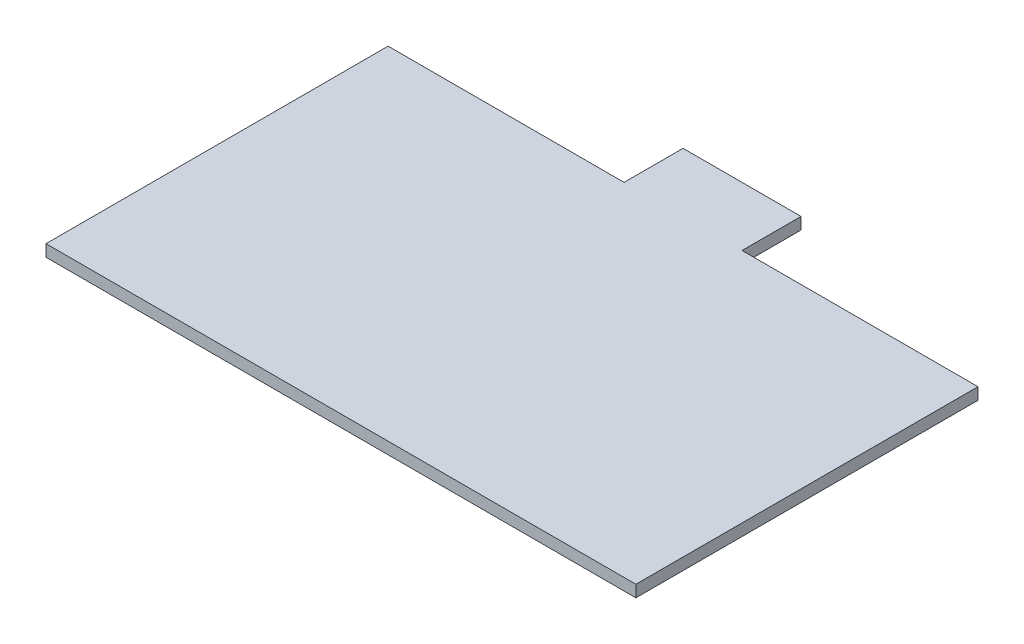
SolidWorks part; units mm, degrees
ref_plane "Front Plane" through (0, 0, 0) normal (0, 0, 1) x (1, 0, 0)
ref_plane "Top Plane" through (0, 0, 0) normal (0, 1, 0) x (1, 0, 0)
ref_plane "Right Plane" through (0, 0, 0) normal (1, 0, 0) x (0, 0, -1)
sketch "Sketch1" plane through (0, 0, 0) normal (0, 1, 0) x (1, 0, 0)
  line L1 (25, -14.5) -> (-25, -14.5)
  line L2 (25, -14.5) -> (25, 14.5)
  line L3 (25, 14.5) -> (-25, 14.5)
  line L4 (-25, -14.5) -> (-25, 14.5)
  line L5 (25, -14.5) -> (-25, 14.5) construction
  line L6 (25, 14.5) -> (-25, -14.5) construction
  line L7 (-5, 19.5) -> (5, 19.5)
  line L8 (-5, 19.5) -> (-5, 14.5)
  line L9 (-5, 14.5) -> (5, 14.5)
  line L10 (5, 19.5) -> (5, 14.5)
  point P0 (0, 0)
  point P10 (5, 17)
  dimension "D1" = 50
  dimension "D2" = 29
  dimension "D3" = 10
  dimension "D4" = 20
  dimension "D5" = 0
  dimension "D6" = 5
extrude "Boss-Extrude4" add sketch "Sketch1" along normal blind 1 contours L10 L7 L8 L3 | L4 L1 L2 L3
sketch "Sketch2" plane through (0, 1, 0) normal (0, 1, 0) x (1, 0, 0)
  line L0 (-5, 19.5) -> (-5, 14.5) construction
  line L1 (-5, 19.5) -> (5, 19.5)
  line L2 (-5, 19.5) -> (-5, 14.5)
  line L3 (-5, 14.5) -> (5, 14.5)
  line L4 (5, 19.5) -> (5, 14.5)
  line L5 (5, 19.5) -> (5, 14.5) construction
  line L6 (-5, 19.5) -> (5, 19.5) construction
  line L7 (-5, 14.5) -> (-25, 14.5) construction
  dimension "D1" = 0
  dimension "D2" = 0
  dimension "D3" = 0
  dimension "D4" = 0
